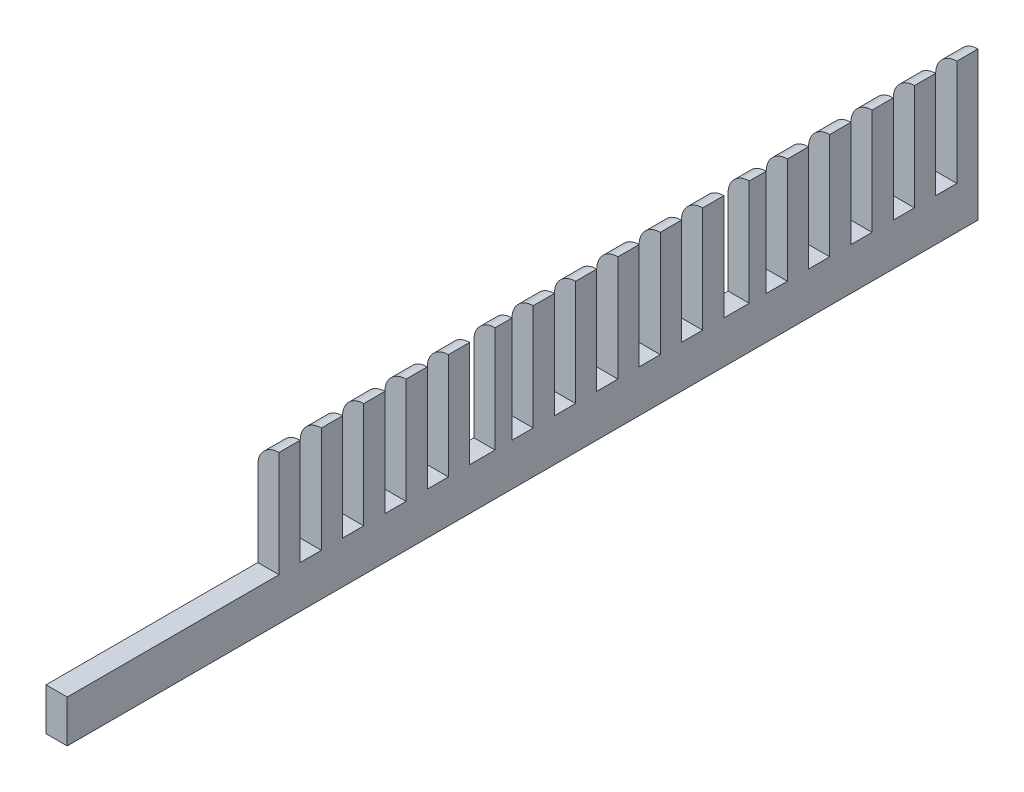
SolidWorks part; units mm, degrees
material "AISI 1020"
ref_plane "Alzado" through (0, 0, 0) normal (0, 0, 1) x (1, 0, 0)
ref_plane "Planta" through (0, 0, 0) normal (0, 1, 0) x (1, 0, 0)
ref_plane "Vista lateral" through (0, 0, 0) normal (1, 0, 0) x (0, 0, -1)
sketch "Croquis1" plane through (0, 0, 0) normal (0, 0, 1) x (1, 0, 0)
  line L1 (-2.5, -17.5) -> (2.5, -17.5)
  line L2 (-2.5, -17.5) -> (-2.5, 12.5)
  line L4 (2.5, -17.5) -> (2.5, 17.5)
  line L5 (-2.5, -17.5) -> (2.5, 17.5) construction
  line L6 (-2.0742, 14.5192) -> (2.5, -17.5) construction
  arc A0 (2.5, 17.5) -> (-2.5, 12.5) centre (2.5, 12.5) ccw
  point P0 (0, 0)
extrude "Saliente-Extruir1" add sketch "Croquis1" along normal mid plane 170
sketch "Croquis2" plane through (2.5, 0, 0) normal (1, 0, 0) x (0, 0, -1)
  line L0 (-85, 17.5) -> (85, 17.5) construction
  line L1 (75, 17.5) -> (80, 17.5)
  line L2 (75, 17.5) -> (75, -7.5)
  line L3 (75, -7.5) -> (80, -7.5)
  line L4 (80, 17.5) -> (80, -7.5)
  line L5 (85, -17.5) -> (85, 17.5) construction
  line L6 (-85, -17.5) -> (85, -17.5) construction
  line L7 (65, 17.5) -> (65, -7.5)
  line L8 (65, -7.5) -> (70, -7.5)
  line L9 (70, 17.5) -> (70, -7.5)
  line L10 (65, 17.5) -> (70, 17.5)
  line L11 (55, 17.5) -> (55, -7.5)
  line L12 (55, -7.5) -> (60, -7.5)
  line L13 (60, 17.5) -> (60, -7.5)
  line L14 (55, 17.5) -> (60, 17.5)
  line L15 (45, 17.5) -> (45, -7.5)
  line L16 (45, -7.5) -> (50, -7.5)
  line L17 (50, 17.5) -> (50, -7.5)
  line L18 (45, 17.5) -> (50, 17.5)
  line L19 (35, 17.5) -> (35, -7.5)
  line L20 (35, -7.5) -> (40, -7.5)
  line L21 (40, 17.5) -> (40, -7.5)
  line L22 (35, 17.5) -> (40, 17.5)
  line L23 (25, 17.5) -> (25, -7.5)
  line L24 (25, -7.5) -> (30, -7.5)
  line L25 (30, 17.5) -> (30, -7.5)
  line L26 (25, 17.5) -> (30, 17.5)
  line L27 (15, 17.5) -> (15, -7.5)
  line L28 (15, -7.5) -> (20, -7.5)
  line L29 (20, 17.5) -> (20, -7.5)
  line L30 (15, 17.5) -> (20, 17.5)
  line L31 (5, 17.5) -> (5, -7.5)
  line L32 (5, -7.5) -> (10, -7.5)
  line L33 (10, 17.5) -> (10, -7.5)
  line L34 (5, 17.5) -> (10, 17.5)
  line L35 (-5, 17.5) -> (-5, -7.5)
  line L36 (-5, -7.5) -> (0, -7.5)
  line L37 (0, 17.5) -> (0, -7.5)
  line L38 (-5, 17.5) -> (0, 17.5)
  line L39 (-15, 17.5) -> (-15, -7.5)
  line L40 (-15, -7.5) -> (-10, -7.5)
  line L41 (-10, 17.5) -> (-10, -7.5)
  line L42 (-15, 17.5) -> (-10, 17.5)
  line L43 (-25, 17.5) -> (-25, -7.5)
  line L44 (-25, -7.5) -> (-20, -7.5)
  line L45 (-20, 17.5) -> (-20, -7.5)
  line L46 (-25, 17.5) -> (-20, 17.5)
  line L47 (-35, 17.5) -> (-35, -7.5)
  line L48 (-35, -7.5) -> (-30, -7.5)
  line L49 (-30, 17.5) -> (-30, -7.5)
  line L50 (-35, 17.5) -> (-30, 17.5)
  line L51 (-45, 17.5) -> (-45, -7.5)
  line L52 (-45, -7.5) -> (-40, -7.5)
  line L53 (-40, 17.5) -> (-40, -7.5)
  line L54 (-45, 17.5) -> (-40, 17.5)
  line L55 (-55, 17.5) -> (-55, -7.5)
  line L56 (-55, -7.5) -> (-50, -7.5)
  line L57 (-50, 17.5) -> (-50, -7.5)
  line L58 (-55, 17.5) -> (-50, 17.5)
  line L59 (-65, 17.5) -> (-65, -7.5)
  line L60 (-65, -7.5) -> (-60, -7.5)
  line L61 (-60, 17.5) -> (-60, -7.5)
  line L62 (-65, 17.5) -> (-60, 17.5)
  line L63 (-75, 17.5) -> (-75, -7.5)
  line L64 (-75, -7.5) -> (-70, -7.5)
  line L65 (-70, 17.5) -> (-70, -7.5)
  line L66 (-75, 17.5) -> (-70, 17.5)
  line L67 (-85, 17.5) -> (-85, -7.5)
  line L68 (-85, -7.5) -> (-80, -7.5)
  line L69 (-80, 17.5) -> (-80, -7.5)
  line L70 (-85, 17.5) -> (-80, 17.5)
  dimension "D1" = 5
  dimension "D2" = 5
  dimension "D3" = 10
  dimension "D4" = 17
extrude "Cortar-Extruir1" cut sketch "Croquis2" against normal through all
sketch "Croquis3" plane through (0, 0, 85) normal (0, 0, 1) x (1, 0, 0)
  line L1 (-2.5, -17.5) -> (2.5, -17.5)
  line L2 (-2.5, -17.5) -> (-2.5, -7.5)
  line L3 (-2.5, -7.5) -> (2.5, -7.5)
  line L4 (2.5, -17.5) -> (2.5, -7.5)
extrude "Saliente-Extruir2" add sketch "Croquis3" along normal blind 45
sketch "Croquis4" plane through (2.5, 0, 0) normal (1, 0, 0) x (0, 0, -1)
  line L9 (-30, 17.5) -> (-29, 17.5)
  line L10 (-30, 17.5) -> (-30, -7.5)
  line L11 (-30, -7.5) -> (-29, -7.5)
  line L12 (-29, 17.5) -> (-29, -7.5)
  line L14 (30, 17.5) -> (31, 17.5)
  line L15 (30, 17.5) -> (30, -7.5)
  line L16 (30, -7.5) -> (31, -7.5)
  line L17 (31, 17.5) -> (31, -7.5)
  dimension "D1" = 1
  dimension "D3" = 1
extrude "Cortar-Extruir2" cut sketch "Croquis4" against normal through all
